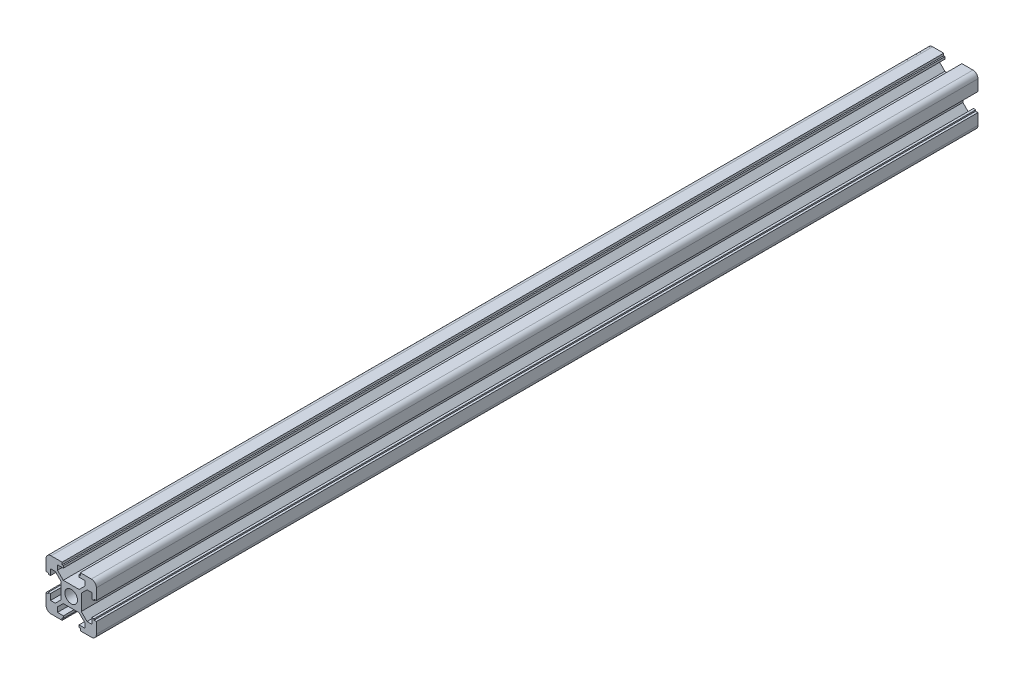
SolidWorks part; units mm, degrees
ref_plane "前视基准面" through (0, 0, 0) normal (0, 0, 1) x (1, 0, 0)
ref_plane "上视基准面" through (0, 0, 0) normal (0, 1, 0) x (1, 0, 0)
ref_plane "右视基准面" through (0, 0, 0) normal (1, 0, 0) x (0, 0, -1)
sketch "草图1" plane through (0, 0, 0) normal (0, 0, 1) x (1, 0, 0)
  line L0 (0, 0) -> (0, 12.7114) construction
  line L1 (0, 0) -> (12.7618, 0) construction
  line L2 (-3.1515, 4) -> (3.1515, 4)
  line L3 (0, 0) -> (12.1278, 12.1278) construction
  line L4 (3.1515, 4) -> (5.45, 6.2985)
  line L5 (5.45, 6.2985) -> (5.45, 8.2)
  line L6 (5.45, 8.2) -> (3.1, 8.2)
  line L7 (3.1, 8.2) -> (3.1, 9.1)
  line L8 (3.1, 9.1) -> (3.6, 9.1)
  line L9 (3.6, 9.1) -> (3.6, 10)
  line L10 (3.6, 10) -> (10, 10)
  line L11 (10, 3.6) -> (10, 10)
  line L12 (9.1, 3.6) -> (10, 3.6)
  line L13 (9.1, 3.1) -> (9.1, 3.6)
  line L14 (8.2, 3.1) -> (9.1, 3.1)
  line L15 (8.2, 5.45) -> (8.2, 3.1)
  line L16 (6.2985, 5.45) -> (8.2, 5.45)
  line L17 (4, 3.1515) -> (6.2985, 5.45)
  line L18 (4, -3.1515) -> (4, 3.1515)
  line L19 (4, -3.1515) -> (6.2985, -5.45)
  line L20 (6.2985, -5.45) -> (8.2, -5.45)
  line L21 (8.2, -5.45) -> (8.2, -3.1)
  line L22 (8.2, -3.1) -> (9.1, -3.1)
  line L23 (9.1, -3.1) -> (9.1, -3.6)
  line L24 (9.1, -3.6) -> (10, -3.6)
  line L25 (10, -3.6) -> (10, -10)
  line L26 (3.6, -10) -> (10, -10)
  line L27 (3.6, -9.1) -> (3.6, -10)
  line L28 (3.1, -9.1) -> (3.6, -9.1)
  line L29 (3.1, -8.2) -> (3.1, -9.1)
  line L30 (5.45, -8.2) -> (3.1, -8.2)
  line L31 (5.45, -6.2985) -> (5.45, -8.2)
  line L32 (3.1515, -4) -> (5.45, -6.2985)
  line L33 (-3.1515, -4) -> (3.1515, -4)
  line L34 (-3.1515, -4) -> (-5.45, -6.2985)
  line L35 (-5.45, -6.2985) -> (-5.45, -8.2)
  line L36 (-5.45, -8.2) -> (-3.1, -8.2)
  line L37 (-3.1, -8.2) -> (-3.1, -9.1)
  line L38 (-3.1, -9.1) -> (-3.6, -9.1)
  line L39 (-3.6, -9.1) -> (-3.6, -10)
  line L40 (-3.6, -10) -> (-10, -10)
  line L41 (-10, -3.6) -> (-10, -10)
  line L42 (-9.1, -3.6) -> (-10, -3.6)
  line L43 (-9.1, -3.1) -> (-9.1, -3.6)
  line L44 (-8.2, -3.1) -> (-9.1, -3.1)
  line L45 (-8.2, -5.45) -> (-8.2, -3.1)
  line L46 (-6.2985, -5.45) -> (-8.2, -5.45)
  line L47 (-4, -3.1515) -> (-6.2985, -5.45)
  line L48 (-4, -3.1515) -> (-4, 3.1515)
  line L49 (-4, 3.1515) -> (-6.2985, 5.45)
  line L50 (-6.2985, 5.45) -> (-8.2, 5.45)
  line L51 (-8.2, 5.45) -> (-8.2, 3.1)
  line L52 (-8.2, 3.1) -> (-9.1, 3.1)
  line L53 (-9.1, 3.1) -> (-9.1, 3.6)
  line L54 (-9.1, 3.6) -> (-10, 3.6)
  line L55 (-10, 3.6) -> (-10, 10)
  line L56 (-3.6, 10) -> (-10, 10)
  line L57 (-3.6, 9.1) -> (-3.6, 10)
  line L58 (-3.1, 9.1) -> (-3.6, 9.1)
  line L59 (-3.1, 8.2) -> (-3.1, 9.1)
  line L60 (-5.45, 8.2) -> (-3.1, 8.2)
  line L61 (-5.45, 6.2985) -> (-5.45, 8.2)
  line L62 (-3.1515, 4) -> (-5.45, 6.2985)
  circle A0 centre (0, 0) radius 2.5
  point P5 (-4, 0)
  point P24 (4, 0)
  point P40 (0, -4)
  point P69 (0, 4)
  dimension "D9" = 5
  dimension "D1" = 4
  dimension "D2" = 0.6
  dimension "D3" = 5.45
  dimension "D4" = 8.2
  dimension "D5" = 3.1
  dimension "D6" = 3.6
  dimension "D7" = 0.9
  dimension "D8" = 1.8
extrude "凸台-拉伸1" add sketch "草图1" along normal blind 350
fillet "圆角1" radius 2 4 edges at (10, -10, 175) (-10, -10, 175) (-10, 10, 175) (10, 10, 175)
